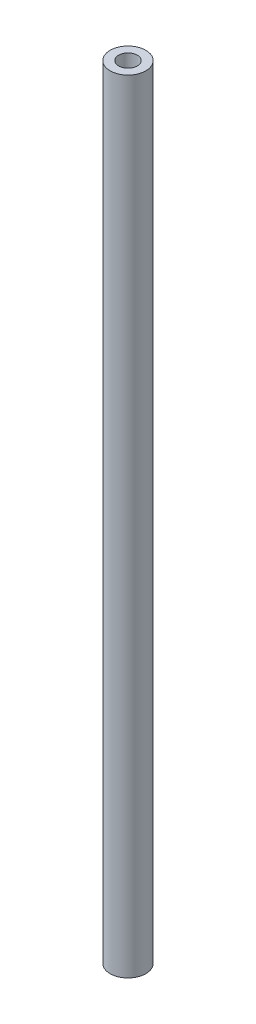
SolidWorks part; units mm, degrees
material "ｽﾃﾝﾚｽ鋼(鋳造)"
ref_plane "正面" through (0, 0, 0) normal (0, 0, 1) x (1, 0, 0)
ref_plane "平面" through (0, 0, 0) normal (0, 1, 0) x (1, 0, 0)
ref_plane "右側面" through (0, 0, 0) normal (1, 0, 0) x (0, 0, -1)
sketch "ｽｹｯﾁ1" plane through (0, 0, 0) normal (0, 1, 0) x (1, 0, 0)
  circle A0 centre (0, 0) radius 4
extrude "ﾎﾞｽ - 押し出し1" add sketch "ｽｹｯﾁ1" along normal blind 175.5
sketch "ｽｹｯﾁ2" plane through (0, 175.5, 0) normal (0, 1, 0) x (1, 0, 0)
  circle A0 centre (0, 0) radius 2.1
extrude "ｶｯﾄ - 押し出し1" cut sketch "ｽｹｯﾁ2" against normal blind 6
sketch "ｽｹｯﾁ3" plane through (0, 0, 0) normal (0, -1, 0) x (1, 0, 0)
  circle A0 centre (0, 0) radius 2.1
extrude "ｶｯﾄ - 押し出し2" cut sketch "ｽｹｯﾁ3" against normal blind 6
